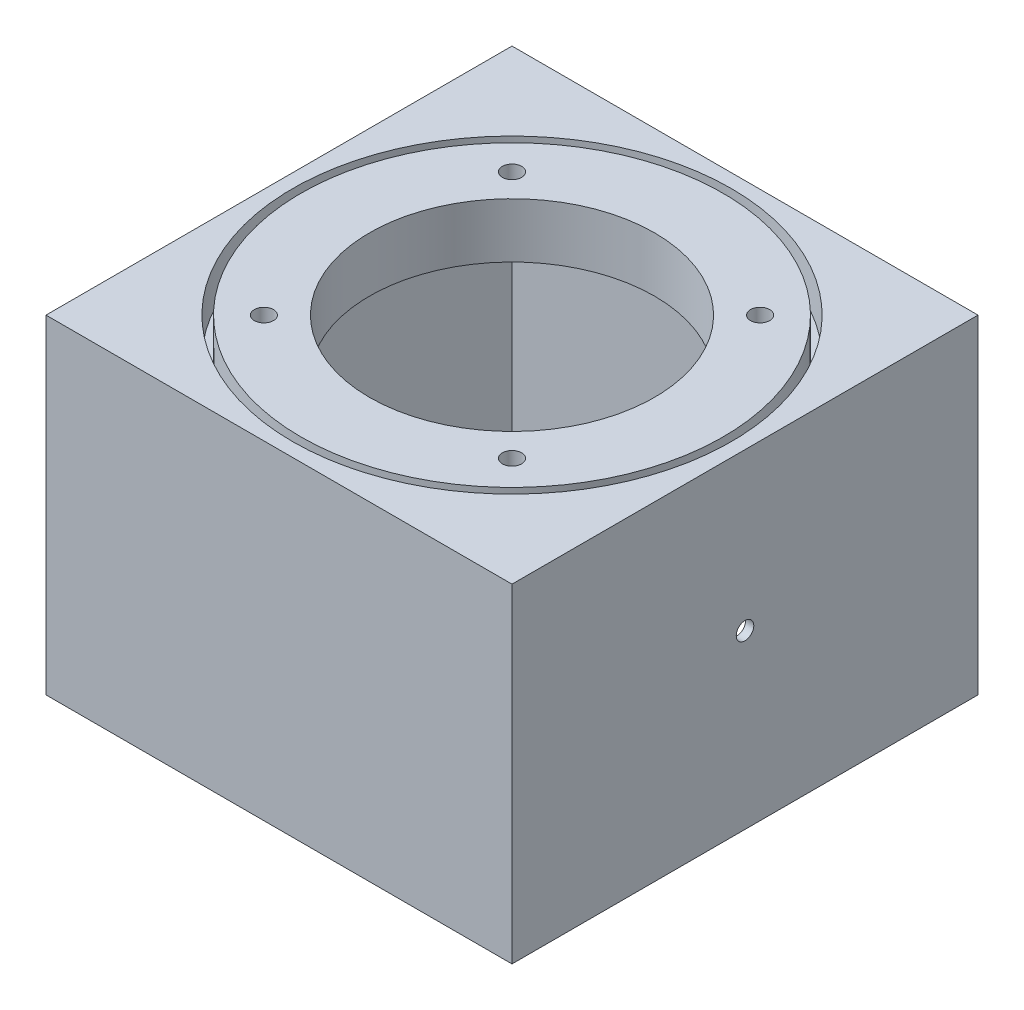
SolidWorks part; units mm, degrees
ref_plane "Płaszczyzna przednia" through (0, 0, 0) normal (0, 0, 1) x (1, 0, 0)
ref_plane "Płaszczyzna górna" through (0, 0, 0) normal (0, 1, 0) x (1, 0, 0)
ref_plane "Płaszczyzna prawa" through (0, 0, 0) normal (1, 0, 0) x (0, 0, -1)
sketch "Sketch1" plane through (0, 0, 0) normal (0, 1, 0) x (1, 0, 0)
  line L1 (-42.5, -42.5) -> (42.5, -42.5)
  line L2 (-42.5, -42.5) -> (-42.5, 42.5)
  line L3 (-42.5, 42.5) -> (42.5, 42.5)
  line L4 (42.5, -42.5) -> (42.5, 42.5)
  line L5 (-42.5, -42.5) -> (42.5, 42.5) construction
  line L6 (-42.5, 42.5) -> (42.5, -42.5) construction
  circle A0 centre (0, 0) radius 26
  dimension "D1" = 52
  dimension "D2" = 85
  dimension "D3" = 85
extrude "Boss-Extrude1" add sketch "Sketch1" along normal blind 10
sketch "Sketch2" plane through (0, 10, 0) normal (0, 1, 0) x (1, 0, 0)
  line L0 (-42.5, -42.5) -> (42.5, 42.5) construction
  line L1 (-42.5, 42.5) -> (42.5, -42.5) construction
  circle A0 centre (22.6281, 22.6281) radius 1.75
  circle A1 centre (-22.6268, 22.6268) radius 1.75
  circle A2 centre (-22.6268, -22.6268) radius 1.75
  circle A3 centre (22.6281, -22.6281) radius 1.75
  point P5 (0, 0)
  point P10 (0, 0)
  dimension "D1" = 3.5
  dimension "D2" = 3.5
  dimension "D3" = 3.5
  dimension "D4" = 3.5
  dimension "D5" = 64
  dimension "D6" = 64
  dimension "D7" = 28.105
  dimension "D8" = 28.1032
  dimension "D9" = 28.105
  dimension "D10" = 28.1032
extrude "Cut-Extrude1" cut sketch "Sketch2" against normal through all
sketch "Sketch3" plane through (0, 0, 0) normal (0, -1, 0) x (-1, 0, 0)
  line L1 (-42.5, -42.5) -> (42.5, -42.5)
  line L2 (-42.5, -42.5) -> (-42.5, 42.5)
  line L3 (-42.5, 42.5) -> (42.5, 42.5)
  line L4 (42.5, -42.5) -> (42.5, 42.5)
  line L5 (-42.5, -42.5) -> (42.5, 42.5) construction
  line L6 (-42.5, 42.5) -> (42.5, -42.5) construction
  line L7 (-41, -41) -> (41, -41)
  line L8 (-41, -41) -> (-41, 41)
  line L9 (-41, 41) -> (41, 41)
  line L10 (41, -41) -> (41, 41)
  line L11 (-41, -41) -> (41, 41) construction
  line L12 (-41, 41) -> (41, -41) construction
  point P0 (0, 0)
  point P7 (0, 0)
  dimension "D1" = 1.5
  dimension "D2" = 1.5
  dimension "D3" = 1.5
  dimension "D4" = 1.5
  dimension "D5" = 82
extrude "Boss-Extrude2" add sketch "Sketch3" along normal blind 50
sketch "Sketch4" plane through (-42.5, 0, 0) normal (-1, 0, 0) x (0, 0, 1)
  line L0 (41, 0) -> (-41, 0) construction
  line L1 (42.5, 10) -> (42.5, -50) construction
  line L2 (-42.5, 10) -> (-42.5, -50) construction
  circle A0 centre (0, -18.6) radius 1.6
  dimension "D1" = 3.2
  dimension "D2" = 18.6
  dimension "D4" = 42.5
  dimension "D3" = 42.5
extrude "Cut-Extrude2" cut sketch "Sketch4" against normal through all
sketch "Sketch5" plane through (0, 10, 0) normal (0, 1, 0) x (1, 0, 0)
  circle A0 centre (0, 0) radius 40
  circle A1 centre (0, 0) radius 38.5
  dimension "D1" = 80
  dimension "D2" = 77
extrude "Cut-Extrude3" cut sketch "Sketch5" against normal blind 7
